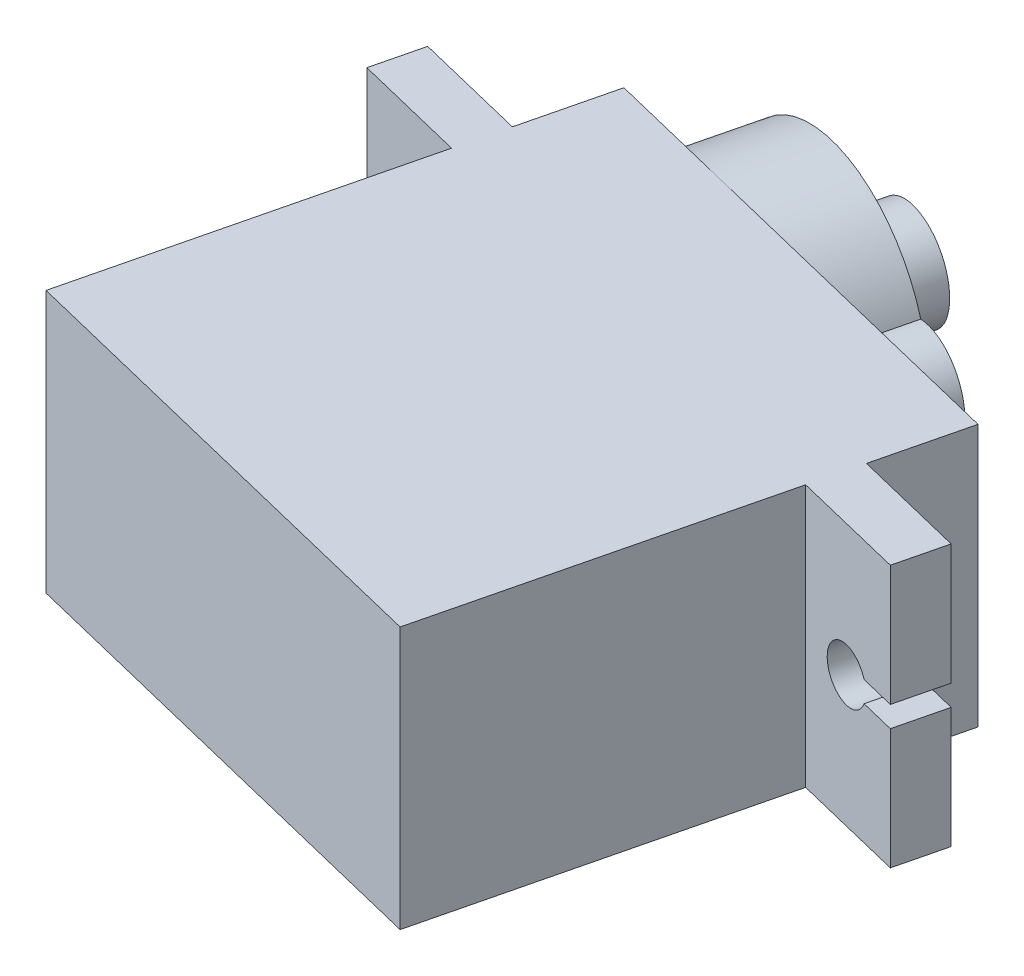
SolidWorks part; units mm, degrees
ref_plane "Front Plane" through (0, 0, 0) normal (0, 0, 1) x (1, 0, 0)
ref_plane "Top Plane" through (0, 0, 0) normal (0, 1, 0) x (1, 0, 0)
ref_plane "Right Plane" through (0, 0, 0) normal (1, 0, 0) x (0, 0, -1)
sketch "Sketch1" plane through (0, 0, 0) normal (0, 1, 0) x (1, 0, 0)
  line L0 (-7.1974, -11.7066) -> (15.146, -17.1633)
  line L1 (15.146, -17.1633) -> (18.9419, -1.6202)
  line L2 (-7.1974, -11.7066) -> (-3.4014, 3.8366)
  line L3 (18.9419, -1.6202) -> (24.2849, -2.925)
  line L4 (-3.4014, 3.8366) -> (-8.7444, 5.1414)
  line L5 (24.2849, -2.925) -> (24.8543, -0.5935)
  line L6 (-8.7444, 5.1414) -> (-8.175, 7.4729)
  line L7 (24.8543, -0.5935) -> (19.5113, 0.7113)
  line L8 (-8.175, 7.4729) -> (-2.832, 6.168)
  line L9 (-2.832, 6.168) -> (-1.7881, 10.4424)
  line L10 (19.5113, 0.7113) -> (20.5552, 4.9857)
  line L11 (20.5552, 4.9857) -> (-1.7881, 10.4424)
extrude "Boss-Extrude1" add sketch "Sketch1" along normal blind 12.5
sketch "Sketch2" plane through (2.3061, 0, -9.4425) normal (0.2372, 0, -0.9714) x (-0.9714, 0, -0.2372)
  line L0 (4.2145, 6.25) -> (-2.0355, 6.25)
  line L1 (4.2145, 12.5) -> (4.2145, 0) construction
  circle A0 centre (-2.0355, 6.25) radius 6.25
  circle A1 centre (-8.2855, 6.25) radius 2.4
extrude "Boss-Extrude2" add sketch "Sketch2" along normal blind 4.4
sketch "Sketch3" plane through (3.35, 0, -13.7169) normal (0.2372, 0, -0.9714) x (-0.9714, 0, -0.2372)
  line L0 (-2.0355, 12.5) -> (-2.0355, 6.25)
  arc A0 (-7.8247, 3.8947) -> (-7.8247, 8.6053) centre (-2.0355, 6.25) ccw construction
  circle A1 centre (-2.0355, 6.25) radius 2.4
extrude "Boss-Extrude3" add sketch "Sketch3" along normal blind 3.2
sketch "Sketch4" plane through (1.2622, 0, -5.1682) normal (0.2372, 0, -0.9714) x (-0.9714, 0, -0.2372)
  line L0 (-18.7855, 6.25) -> (-21.4355, 6.25)
  line L1 (-18.7855, 12.5) -> (-18.7855, 0) construction
  line L2 (-24.2855, 6.25) -> (-24.2855, 6.75)
  line L3 (-24.2855, 12.5) -> (-24.2855, 0) construction
  line L4 (-24.2855, 6.25) -> (-24.2855, 5.75)
  line L5 (-24.2855, 5.75) -> (-22.5812, 5.75)
  line L6 (-24.2855, 6.75) -> (-22.5812, 6.75)
  line L7 (-22.5812, 6.75) -> (-22.5812, 5.75)
  circle A0 centre (-21.4355, 6.25) radius 1.25
extrude "Cut-Extrude1" cut sketch "Sketch4" against normal blind 3.2
sketch "Sketch5" plane through (1.2622, 0, -5.1682) normal (0.2372, 0, -0.9714) x (-0.9714, 0, -0.2372)
  line L0 (4.2145, 6.25) -> (6.8645, 6.25)
  line L1 (4.2145, 12.5) -> (4.2145, 0) construction
  line L2 (6.8645, 6.25) -> (9.7145, 6.25)
  line L3 (9.7145, 12.5) -> (9.7145, 0) construction
  line L4 (9.7145, 6.25) -> (9.7145, 6.75)
  line L5 (9.7145, 6.25) -> (9.7145, 5.75)
  line L6 (9.7145, 5.75) -> (7.8793, 5.75)
  line L7 (7.8793, 5.75) -> (7.8793, 6.75)
  line L8 (7.8793, 6.75) -> (9.7145, 6.75)
  circle A0 centre (6.8645, 6.25) radius 1.5757
  line M2 (9.7145, 0) -> (9.7145, 12.5)
extrude "Cut-Extrude2" cut sketch "Sketch5" against normal blind 3.2 contours L8 A0 L0 L2 L7 | L0 A0 L6 L7 L2 | A0 L6 L2 M2 | A0 L2 L8 M2 | L2 A0 L8 L7 | L6 A0 L2 L7
